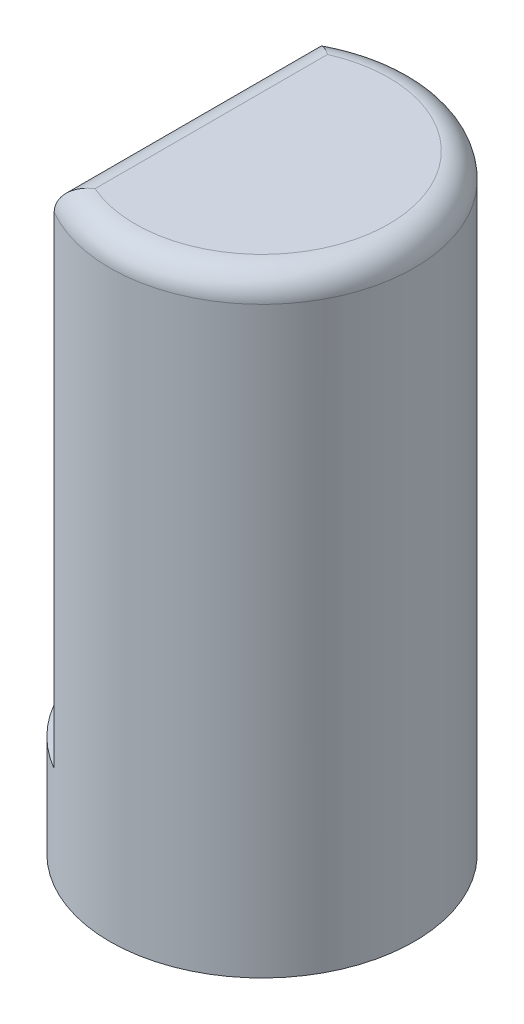
SolidWorks part; units mm, degrees
material "1060 Alloy"
ref_plane "Front Plane" through (0, 0, 0) normal (0, 0, 1) x (1, 0, 0)
ref_plane "Top Plane" through (0, 0, 0) normal (0, 1, 0) x (1, 0, 0)
ref_plane "Right Plane" through (0, 0, 0) normal (1, 0, 0) x (0, 0, -1)
sketch "Sketch1" plane through (0, 0, 0) normal (0, 1, 0) x (1, 0, 0)
  circle A0 centre (0, 0) radius 3
  dimension "D1" = 6
extrude "Boss-Extrude1" add sketch "Sketch1" along normal blind 12
sketch "Sketch4" plane through (0, 12, 0) normal (0, 1, 0) x (1, 0, 0)
  line L0 (-1.5, 2.5981) -> (-1.5, -2.5981)
  line L1 (-1.5, 2.5981) -> (-4.7176, 2.5981)
  line L2 (-4.7176, 2.5981) -> (-4.7176, -2.5981)
  line L3 (-4.7176, -2.5981) -> (-1.5, -2.5981)
  circle A0 centre (0, 0) radius 3 construction
  dimension "D1" = 1.5
extrude "Cut-Extrude1" cut sketch "Sketch4" against normal blind 10
fillet "Fillet1" radius 0.5 2 edges at (3, 12, 0) (-1.5, 12, 0)
